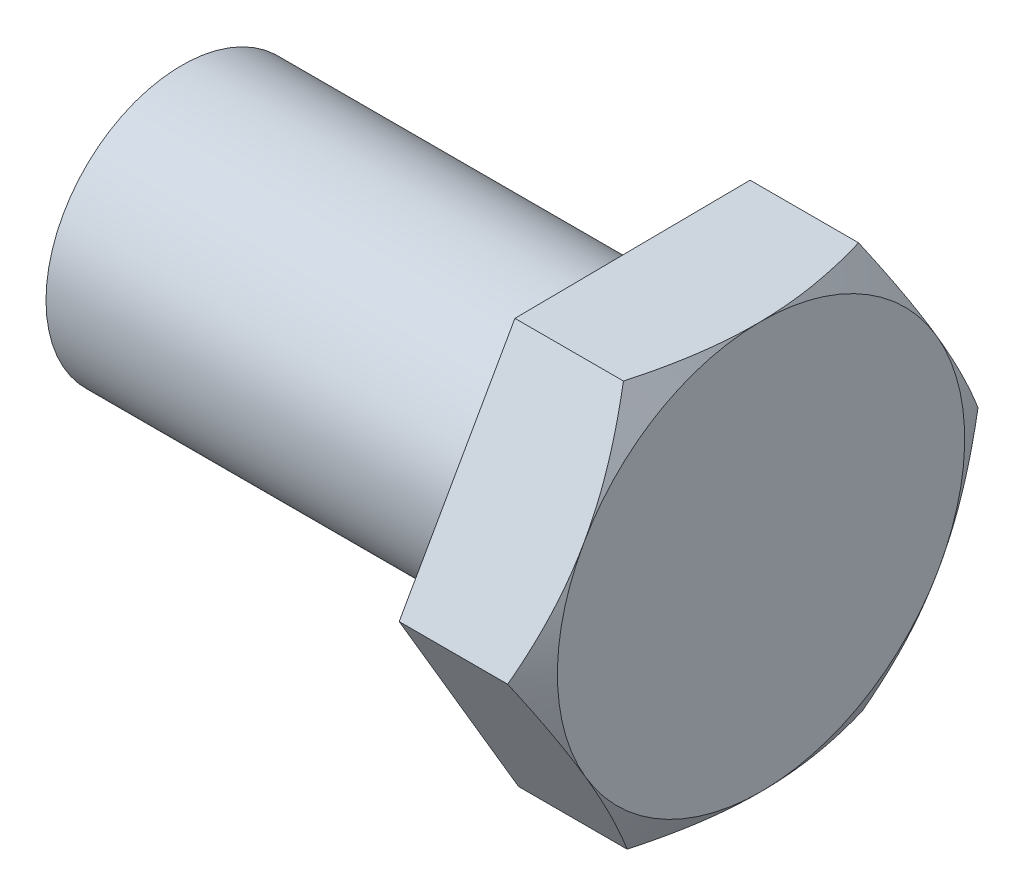
SolidWorks part; units mm, degrees
ref_plane "Front Plane" through (0, 0, 0) normal (0, 0, 1) x (1, 0, 0)
ref_plane "Top Plane" through (0, 0, 0) normal (0, 1, 0) x (1, 0, 0)
ref_plane "Right Plane" through (0, 0, 0) normal (1, 0, 0) x (0, 0, -1)
sketch "Sketch1" plane through (0, 0, 0) normal (1, 0, 0) x (0, 0, -1)
  line L1 (8.377, -14.2127) -> (16.4971, 0.1484)
  line L2 (16.4971, 0.1484) -> (8.1201, 14.3611)
  line L3 (8.1201, 14.3611) -> (-8.377, 14.2127)
  line L4 (-8.377, 14.2127) -> (-16.4971, -0.1484)
  line L5 (-16.4971, -0.1484) -> (-8.1201, -14.3611)
  line L6 (-8.1201, -14.3611) -> (8.377, -14.2127)
  circle A0 centre (0, 0) radius 14.2875 construction
  dimension "D1" = 28.575
extrude "Boss-Extrude1" add sketch "Sketch1" along normal blind 8.89
sketch "Sketch2" plane through (8.89, 0, 0) normal (1, 0, 0) x (0, 0, -1)
  circle A0 centre (0, 0) radius 14.2875
  dimension "D1" = 28.575
extrude "Cut-Extrude1" cut sketch "Sketch2" against normal blind 5.08 draft 60 flip side to cut
sketch "Sketch3" plane through (0, 0, 0) normal (-1, 0, 0) x (0, 0, 1)
  circle A0 centre (0, 0) radius 9.525
  dimension "D1" = 19.05
extrude "Boss-Extrude2" add sketch "Sketch3" along normal blind 31.75
